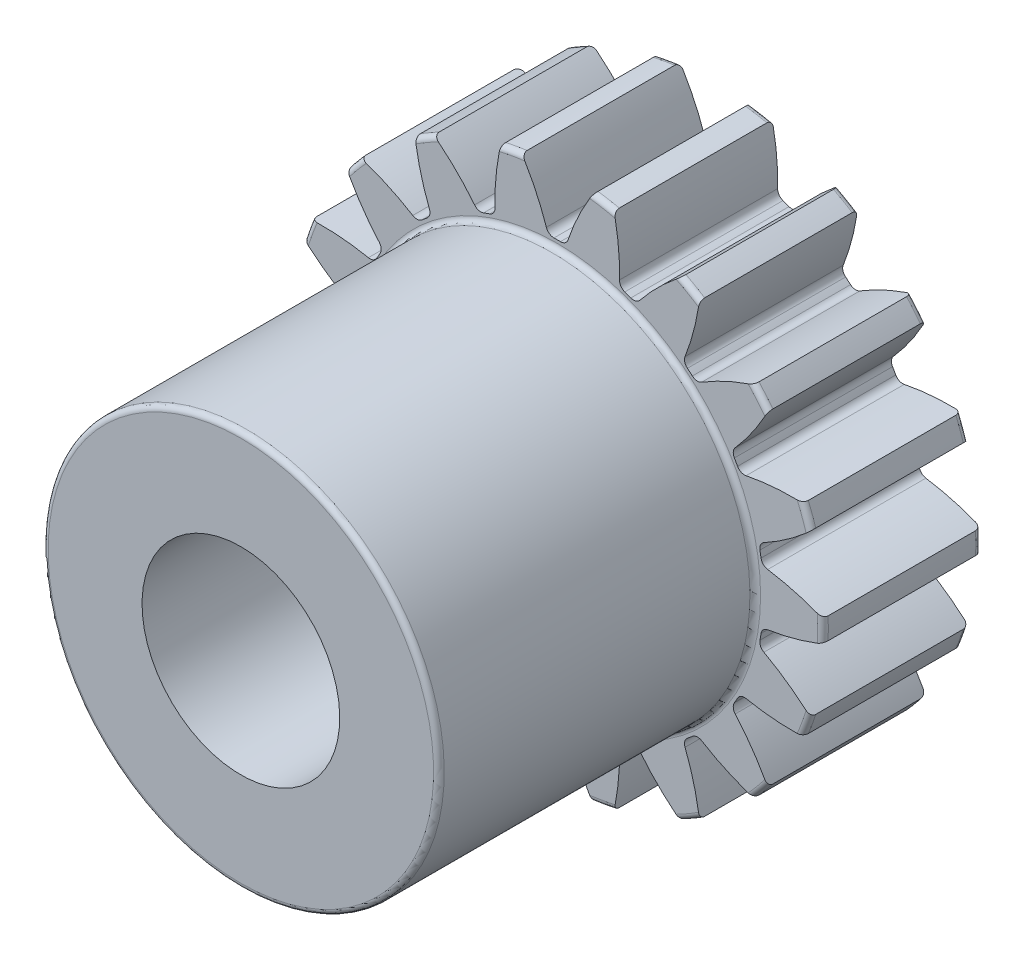
SolidWorks part; units mm, degrees
ref_plane "Front Plane" through (0, 0, 0) normal (0, 0, 1) x (1, 0, 0)
ref_plane "Top Plane" through (0, 0, 0) normal (0, 1, 0) x (1, 0, 0)
ref_plane "Right Plane" through (0, 0, 0) normal (1, 0, 0) x (0, 0, -1)
sketch "Sketch1" plane through (0, 0, 0) normal (0, 0, 1) x (1, 0, 0)
  line L0 (-228.6, 0) -> (228.6, 0) construction
  circle A0 centre (0, 0) radius 5.334 construction
  circle A1 centre (0, 0) radius 4.7625 construction
  circle A2 centre (0, 0) radius 4.1434 construction
  circle A3 centre (0, 0) radius 3.9751 construction
  circle A4 centre (0, 0) radius 1.9844 construction
  dimension "D2" = 0.5715
  dimension "D3" = 1.1906
  dimension "D1" = 1.1906
sketch "Sketch2" plane through (0, 0, 0) normal (1, 0, 0) x (0, 0, -1)
  line L0 (0, 0) -> (-3.175, 0) construction
  line L1 (-3.175, 0) -> (-9.525, 0) construction
  dimension "Overall Width" = 9.525
  dimension "Face Width" = 3.175
sketch "Sketch4" plane through (0, 0, 0) normal (1, 0, 0) x (0, 0, -1)
  line L0 (-9.525, 1.9844) -> (-9.525, 3.9751)
  line L1 (-9.525, 3.9751) -> (-3.175, 3.9751)
  line L2 (-3.175, 3.9751) -> (-3.175, 5.334)
  line L3 (-3.175, 5.334) -> (0, 5.334)
  line L4 (0, 5.334) -> (0, 1.9844)
  line L5 (-3.175, 3.9751) -> (-3.175, 0) construction
  line L6 (0, 5.334) -> (0, -5.334) construction
  line L7 (-3.175, 3.9751) -> (0, 3.9751) construction
  line L12 (-9.525, 1.9844) -> (0, 1.9844)
revolve "Revolve1" add sketch "Sketch4" angle 360 about L1
fillet "Fillet2" radius 0.1067 4 edges at (0, 3.9751, 9.525) (0, 3.9751, 3.175) (0, 5.334, 3.175) (0, 5.334, 0)
sketch "Sketch7" plane through (0, 0, 3.175) normal (0, 0, 1) x (1, 0, 0)
  line L0 (0, 0) -> (0, 5.334) construction
  line L1 (0.4151, 4.7444) -> (0.6703, 5.2917) construction
  line L3 (0.9262, 5.253) -> (0.827, 4.6901) construction
  line L4 (0.827, 4.6901) -> (0.7195, 4.0804) construction
  line L5 (0, 0) -> (0.7195, 4.0804) construction
  line L6 (0.4151, 4.7444) -> (0, 0) construction
  line L7 (0.4151, 4.7444) -> (0.4649, 5.3137) construction
  line L8 (0.4151, 4.7444) -> (0, 0) construction
  circle A0 centre (0, 0) radius 5.334 construction
  arc A1 (-0.0648, 4.1429) -> (0.0648, 4.1429) centre (0, 0) cw
  circle A2 centre (0, 0) radius 4.1434 construction
  arc A3 (-0.4151, 4.7444) -> (0.4151, 4.7444) centre (0, 0) cw construction
  circle A4 centre (0, 0) radius 4.7625 construction
  arc A5 (1.139, 5.211) -> (0.712, 5.2863) centre (0, 0) ccw construction
  arc A6 (0.4151, 4.7444) -> (1.2326, 4.6002) centre (0, 0) cw construction
  arc A7 (-0.712, 5.2863) -> (0.712, 5.2863) centre (0, 0) cw
  arc A8 (0.2177, 4.251) -> (0.712, 5.2863) centre (4.7314, 2.7317) cw
  arc A9 (-0.2177, 4.251) -> (-0.712, 5.2863) centre (-4.7314, 2.7317) ccw
  arc A10 (-0.0648, 4.1429) -> (-0.2177, 4.251) centre (-0.0672, 4.3016) cw
  arc A11 (0.0648, 4.1429) -> (0.2177, 4.251) centre (0.0672, 4.3016) ccw
  point P26 (-0.1817, 4.1394)
  point P29 (0.1817, 4.1394)
  dimension "D4" = 0.1588
  dimension "D5" = 4.7625
  dimension "D3" = 20
  dimension "D1" = 1.6624
  dimension "D2" = 0.8312
extrude "Cut-Extrude2" cut sketch "Sketch7" against normal through all
pattern_circular "CirPattern1" count 18 over 360 about axis through (0, 0, 0) along (0, 0, 1) of "Cut-Extrude2"
equation "\"D1@Sketch1\"=2.25*(\"Pitch Dia.@Sketch1\"/\"Number of Teeth@Sketch1\")"
equation "\"D1@CirPattern1\"=\"Number of Teeth@Sketch1\""
equation "\"D1@Fillet2\"=\"OD@Sketch1\"*.01"
equation "\"D1@Sketch7\"=3.14159*(\"Pitch Dia.@Sketch1\"/\"Number of Teeth@Sketch1\")"
equation "\"D2@Sketch7\"=\"D1@Sketch7\"/2"
equation "\"D4@Sketch7\"=\"D1@Sketch7\"*.0955"
equation "\"D5@Sketch7\"=\"Pitch Dia.@Sketch1\"/2"
